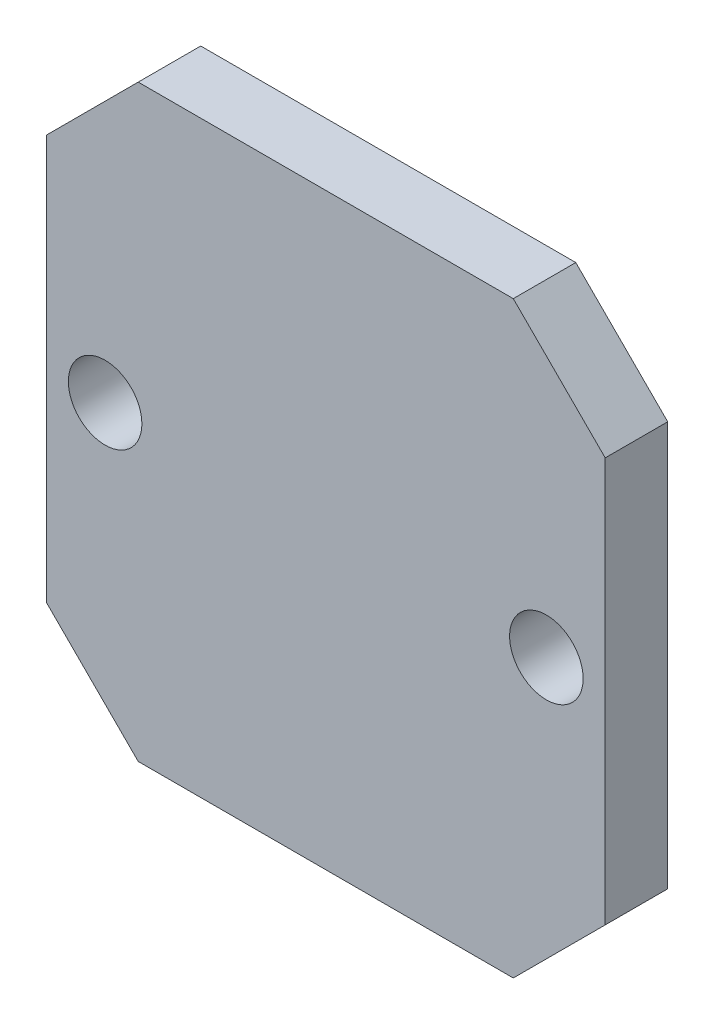
SolidWorks part; units mm, degrees
ref_plane "Plan de face" through (0, 0, 0) normal (0, 0, 1) x (1, 0, 0)
ref_plane "Plan de dessus" through (0, 0, 0) normal (0, 1, 0) x (1, 0, 0)
ref_plane "Plan de droite" through (0, 0, 0) normal (1, 0, 0) x (0, 0, -1)
sketch "Esquisse1" plane through (0, 0, 0) normal (0, 0, 1) x (1, 0, 0)
  line L0 (0, 0) -> (0, 8) construction
  line L1 (7.6, 8) -> (-7.6, 8)
  line L2 (7.6, 8) -> (7.6, -8)
  line L3 (7.6, -8) -> (-7.6, -8)
  line L4 (-7.6, 8) -> (-7.6, -8)
  line L5 (7.6, 8) -> (-7.6, -8) construction
  line L6 (7.6, -8) -> (-7.6, 8) construction
  circle A0 centre (-6, 0) radius 1
  circle A1 centre (6, 0) radius 1
  point P0 (0, 0)
  dimension "D1" = 15.2
  dimension "D2" = 2
  dimension "D3" = 16
  dimension "D4" = 12
extrude "Boss.-Extru.1" add sketch "Esquisse1" along normal blind 1.7
chamfer "Chanfrein1" distance 2.5 angle 45 4 edges at (7.6, -8, 0.85) (-7.6, -8, 0.85) (7.6, 8, 0.85) (-7.6, 8, 0.85)
